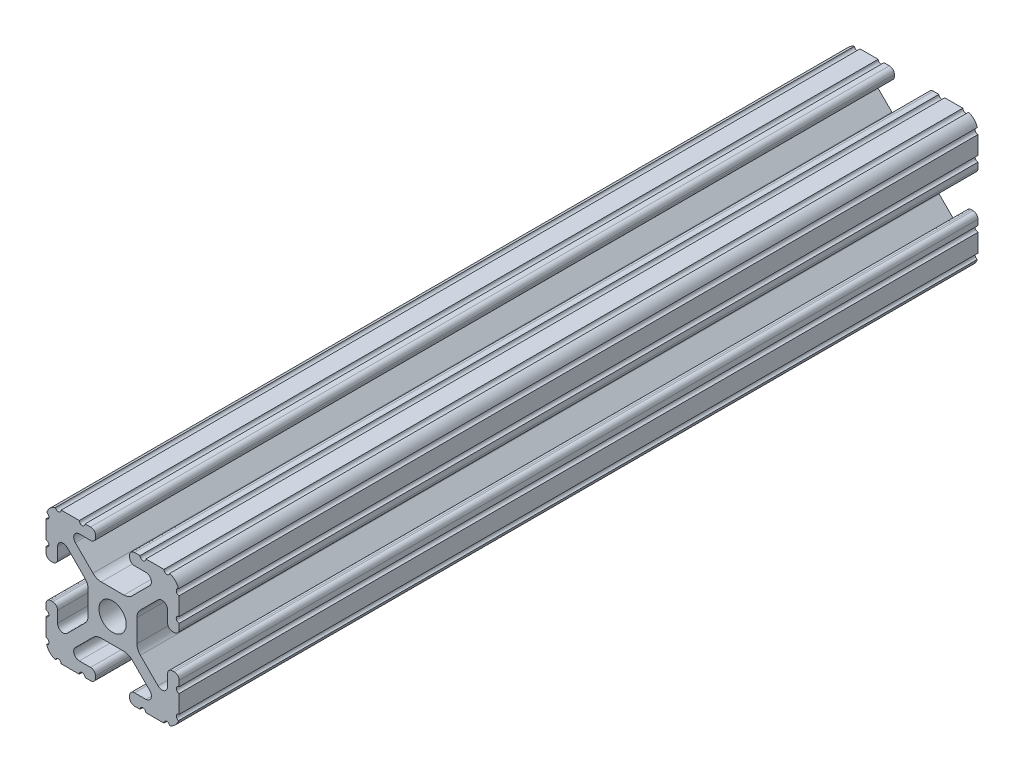
SolidWorks part; units mm, degrees
ref_plane "Front Plane" through (0, 0, 0) normal (0, 0, 1) x (1, 0, 0)
ref_plane "Top Plane" through (0, 0, 0) normal (0, 1, 0) x (1, 0, 0)
ref_plane "Right Plane" through (0, 0, 0) normal (1, 0, 0) x (0, 0, -1)
sketch "Sketch2" plane through (0, 0, 0) normal (0, 0, 1) x (1, 0, 0)
  line L0 (0, 12.7) -> (0, -12.7) construction
  line L1 (-12.7, 0) -> (12.7, 0) construction
  line L2 (3.2512, -12.7) -> (12.7, -12.7)
  line L3 (12.7, -12.7) -> (12.7, -3.2512)
  line L4 (3.2512, -12.7) -> (3.2512, -10.4902)
  line L5 (3.2512, -10.4902) -> (8.9276, -10.4902)
  line L6 (8.9276, -10.4902) -> (3.0856, -4.6482)
  line L7 (0, 0) -> (12.7, -12.7) construction
  line L8 (12.7, -3.2512) -> (10.4902, -3.2512)
  line L9 (10.4902, -3.2512) -> (10.4902, -8.9276)
  line L10 (10.4902, -8.9276) -> (4.6482, -3.0856)
  circle A0 centre (0, 0) radius 2.6035
  arc A1 (6.3485, -10.4902) -> (7.1039, -8.6665) centre (6.3485, -9.4219) ccw construction
  point P8 (0, -4.6482)
  dimension "Center Hole Diameter" = 5.207
  dimension "Rail Height" = 25.4
  dimension "Rail Width" = 25.4
  dimension "T-Slot Width" = 6.5024
  dimension "Slot Inner Width" = 14.8336
  dimension "Thickness" = 2.2098
  dimension "Slot Depth" = 5.842
  dimension "D1" = 2.2098
sketch "Sketch3" plane through (0, 0, 0) normal (1, 0, 0) x (0, 0, -1)
  line L0 (-76.2, -12.7) -> (76.2, -12.7) construction
  line L1 (-50.8, 0) -> (50.8, 0) construction
  dimension "Length" = 152.4
  dimension "D1" = 25.4
sketch "Sketch4" plane through (0, 0, 0) normal (0, 0, 1) x (1, 0, 0)
  line L0 (4.1904, -12.7) -> (10.1173, -12.7)
  line L1 (3.2512, -12.7) -> (12.7, -12.7) construction
  line L2 (3.2512, -12.7) -> (3.2512, -10.4902) construction
  line L3 (3.2512, -10.4902) -> (8.9276, -10.4902) construction
  line L4 (3.2512, -11.4294) -> (3.2512, -11.7608)
  line L5 (4.1904, -10.4902) -> (6.3485, -10.4902)
  line L6 (0, -4.6482) -> (2.164, -4.6482)
  line L7 (8.9276, -10.4902) -> (3.0856, -4.6482) construction
  line L8 (3.7373, -5.2999) -> (7.1039, -8.6665)
  line L9 (12.7, -12.7) -> (12.7, -3.2512) construction
  line L10 (10.4902, -8.9276) -> (4.6482, -3.0856) construction
  line L11 (10.4902, -3.2512) -> (10.4902, -8.9276) construction
  line L12 (10.4902, -6.3485) -> (10.4902, -4.1904)
  line L13 (12.7, -3.2512) -> (10.4902, -3.2512) construction
  line L14 (11.4294, -3.2512) -> (11.7608, -3.2512)
  line L15 (12.7, -4.1904) -> (12.7, -10.1173)
  line L16 (8.6665, -7.1039) -> (5.2999, -3.7373)
  line L17 (4.6482, 0) -> (4.6482, -2.164)
  line L18 (-12.7, 0) -> (12.7, 0) construction
  line L19 (0, -4.6482) -> (0, -2.6035)
  line L20 (0, 12.7) -> (0, -12.7) construction
  line L21 (4.6482, 0) -> (2.6035, 0)
  arc A0 (3.2512, -11.7608) -> (4.1904, -12.7) centre (4.1904, -11.7608) ccw
  arc A2 (3.2512, -11.4294) -> (4.1904, -10.4902) centre (4.1904, -11.4294) cw
  arc A3 (6.3485, -10.4902) -> (7.1039, -8.6665) centre (6.3485, -9.4219) ccw
  arc A4 (2.164, -4.6482) -> (3.7373, -5.2999) centre (2.164, -6.8732) cw
  arc A5 (10.1173, -12.7) -> (12.7, -10.1173) centre (10.1173, -10.1173) ccw
  arc A6 (8.6665, -7.1039) -> (10.4902, -6.3485) centre (9.4219, -6.3485) ccw
  arc A7 (10.4902, -4.1904) -> (11.4294, -3.2512) centre (11.4294, -4.1904) cw
  arc A8 (11.7608, -3.2512) -> (12.7, -4.1904) centre (11.7608, -4.1904) cw
  arc A9 (5.2999, -3.7373) -> (4.6482, -2.164) centre (6.8732, -2.164) cw
  circle A10 centre (0, 0) radius 2.6035 construction
  arc A11 (0, -2.6035) -> (2.6035, 0) centre (0, 0) ccw
  dimension "D1" = 2.5827
  dimension "D2" = 2.225
  dimension "D3" = 0.9392
extrude "Boss-Extrude1" add sketch "Sketch4" along normal mid plane 152.4
sketch "Sketch5" plane through (0, 0, 0) normal (0, 0, 1) x (1, 0, 0)
  line L0 (3.2512, -12.7) -> (12.7, -12.7) construction
  line L1 (4.1904, -10.4902) -> (6.3485, -10.4902) construction
  line L3 (0, 0) -> (12.7, -12.7) construction
  line L4 (6.3485, -10.4902) -> (6.3485, -12.7) construction
  line L5 (8.9276, -10.4902) -> (3.0856, -4.6482) construction
  circle A0 centre (10.3562, -12.7) radius 0.5524
  circle A1 centre (5.796, -12.7) radius 0.5524
  circle A2 centre (12.7, -10.3562) radius 0.5524
  circle A3 centre (12.7, -5.796) radius 0.5524
  point P10 (5.2694, -10.4902)
  point P12 (9.4219, -6.3485)
  dimension "D1" = 1.1049
extrude "Cut-Extrude1" cut sketch "Sketch5" against normal through all both and the other way through all
mirror "Mirror1" about plane through (0, 0, 0) normal (1, 0, 0) of bodies 137 134
mirror "Mirror2" about plane through (0, 0, 0) normal (0, 1, 0) of bodies 135
equation "\"D1@Boss-Extrude1\"=\"Length@Sketch3\""
equation "\"D1@Sketch2\"=\"Thickness@Sketch2\""
equation "\"D2@Sketch4\"=\"Slot Inner Width@Sketch2\"*0.15"
equation "\"D1@Sketch4\"=\"D3@Sketch4\"*2.75"
equation "\"D3@Sketch4\"=\"Thickness@Sketch2\"*0.425"
equation "\"D1@Sketch5\"=\"Thickness@Sketch2\"*0.5"
